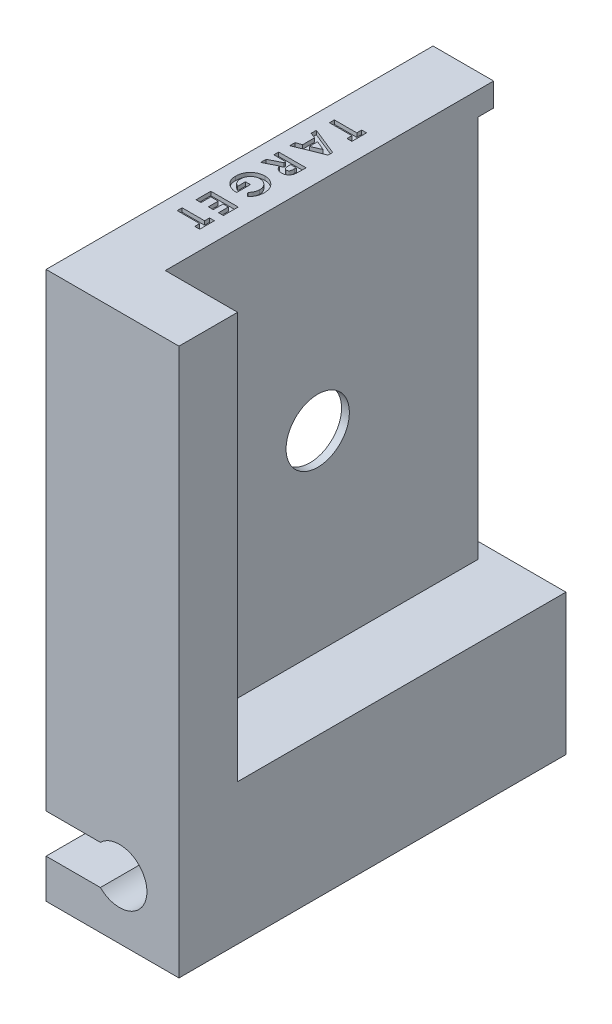
SolidWorks part; units mm, degrees
ref_plane "Plan de face" through (0, 0, 0) normal (0, 0, 1) x (1, 0, 0)
ref_plane "Plan de dessus" through (0, 0, 0) normal (0, 1, 0) x (1, 0, 0)
ref_plane "Plan de droite" through (0, 0, 0) normal (1, 0, 0) x (0, 0, -1)
sketch "Esquisse1" plane through (0, 0, 0) normal (0, 0, 1) x (1, 0, 0)
  line L1 (-8.5, -42.5) -> (8.5, -42.5)
  line L2 (-8.5, -42.5) -> (-8.5, 42.5)
  line L3 (-8.5, 42.5) -> (8.5, 42.5)
  line L4 (8.5, -42.5) -> (8.5, 42.5)
  line L5 (-8.5, -42.5) -> (8.5, 42.5) construction
  line L6 (-8.5, 42.5) -> (8.5, -42.5) construction
  point P0 (0, 0)
  dimension "D1" = 17
  dimension "D2" = 85
extrude "Boss.-Extru.1" add sketch "Esquisse1" along normal blind 49.5
sketch "Esquisse2" plane through (0, 0, 0) normal (0, 0, -1) x (-1, 0, 0)
  line L0 (8.5, 42.5) -> (8.5, -42.5) construction
  line L5 (7.55, 16.25) -> (5.75, 16.25)
  line L6 (7.55, 16.25) -> (7.55, -16.25)
  line L7 (7.55, -16.25) -> (5.75, -16.25)
  line L8 (5.75, 16.25) -> (5.75, -16.25)
  line L9 (7.55, 16.25) -> (5.75, -16.25) construction
  line L10 (7.55, -16.25) -> (5.75, 16.25) construction
  point P0 (6.65, 0)
  dimension "D1" = 1.8
  dimension "D2" = 32.5
  dimension "D3" = 0.95
extrude "Enlèv. mat.-Extru.1" cut sketch "Esquisse2" against normal blind 38.5
sketch "Esquisse3" plane through (0, 0, 0) normal (0, 0, -1) x (-1, 0, 0)
  line L0 (-8.5, -42.5) -> (-8.5, 42.5) construction
  line L1 (8.5, 24.5) -> (-8.5, 24.5)
  line L2 (8.5, 24.5) -> (8.5, -24.5)
  line L3 (8.5, -24.5) -> (-8.5, -24.5)
  line L4 (-8.5, 24.5) -> (-8.5, -24.5)
  line L5 (8.5, 24.5) -> (-8.5, -24.5) construction
  line L6 (8.5, -24.5) -> (-8.5, 24.5) construction
  point P0 (0, 0)
  dimension "D1" = 49
extrude "Enlèv. mat.-Extru.2" cut sketch "Esquisse3" against normal blind 2
sketch "Esquisse4" plane through (-8.5, 0, 0) normal (-1, 0, 0) x (0, 0, 1)
  line L0 (2, -24.5) -> (2, 24.5) construction
  circle A0 centre (22.5, 0) radius 16.25
  dimension "D1" = 32.5
  dimension "D2" = 20.5
extrude "Enlèv. mat.-Extru.3" cut sketch "Esquisse4" against normal through all
sketch "Esquisse5" plane through (-8.5, 0, 0) normal (-1, 0, 0) x (0, 0, 1)
  line L0 (7.0384, -5) -> (2, -5)
  line L1 (2, -24.5) -> (2, 24.5) construction
  line L2 (2, -5) -> (2, 5)
  line L3 (2, 5) -> (7.0384, 5)
  line L4 (7.0384, 5) -> (7.0384, -5)
  line L5 (49.5, -42.5) -> (0, -42.5) construction
  circle A0 centre (22.5, 0) radius 16.25 construction
  dimension "D1" = 10
  dimension "D2" = 37.5
extrude "Enlèv. mat.-Extru.4" cut sketch "Esquisse5" against normal through all
sketch "Esquisse6" plane through (0, 0, 0) normal (0, 0, -1) x (-1, 0, 0)
  line L0 (8.5, -32.5) -> (1.55, -32.5)
  line L1 (8.5, -24.5) -> (8.5, -42.5) construction
  line L2 (8.5, -32.5) -> (8.5, -37.5)
  line L3 (8.5, -37.5) -> (1.55, -37.5)
  line L4 (8.5, -42.5) -> (-8.5, -42.5) construction
  line L5 (-2.04, 0) -> (3.9749, 0) construction
  line L6 (8.5, 32.5) -> (8.5, 37.5)
  line L7 (8.5, 32.5) -> (1.55, 32.5)
  line L8 (8.5, 37.5) -> (1.55, 37.5)
  arc A0 (1.55, -37.5) -> (1.55, -32.5) centre (-0.8995, -35) cw
  arc A1 (1.55, 37.5) -> (1.55, 32.5) centre (-0.8995, 35) ccw
  dimension "D1" = 3.5
  dimension "D2" = 5
  dimension "D3" = 6.95
  dimension "D4" = 6.95
  dimension "D5" = 5
extrude "Enlèv. mat.-Extru.5" cut sketch "Esquisse6" against normal through all
sketch "Esquisse7" plane through (8.5, 0, 0) normal (1, 0, 0) x (0, 0, -1)
  line L5 (-2, 24.5) -> (-42, 24.5)
  line L6 (-2, 24.5) -> (-2, -24.5)
  line L7 (-2, -24.5) -> (-42, -24.5)
  line L8 (-42, 24.5) -> (-42, -24.5)
  dimension "D1" = 49
  dimension "D2" = 40
extrude "Enlèv. mat.-Extru.7" cut sketch "Esquisse7" against normal blind 13.25
sketch "Esquisse9" plane through (-4.75, 0, 0) normal (1, 0, 0) x (0, 0, -1)
  line L7 (-2, 5) -> (-2, 24.5)
  line L8 (-2, 24.5) -> (-42, 24.5)
  line L9 (-42, 24.5) -> (-42, -24.5)
  line L10 (-42, -24.5) -> (-2, -24.5)
  line L11 (-2, -24.5) -> (-2, -5)
  line L12 (-2, -5) -> (-7.0384, -5)
  line L13 (-7.0384, 5) -> (-2, 5)
  line L14 (-2, 5) -> (-2, 24.5)
  line L15 (-2, 24.5) -> (-42, 24.5)
  line L16 (-42, 24.5) -> (-42, -24.5)
  line L17 (-42, -24.5) -> (-2, -24.5)
  line L18 (-2, -24.5) -> (-2, -5)
  line L19 (-2, -5) -> (-7.0384, -5)
  line L20 (-7.0384, 5) -> (-2, 5)
  arc A1 (-7.0384, 5) -> (-7.0384, -5) centre (-22.5, 0) ccw
  arc A2 (-7.0384, 5) -> (-7.0384, -5) centre (-22.5, 0) ccw
  dimension "D1" = 0
extrude "Boss.-Extru.2" add sketch "Esquisse9" along normal blind 3
sketch "Esquisse10" plane through (-1.75, 0, 0) normal (1, 0, 0) x (0, 0, -1)
  line L1 (-2, -24.5) -> (-42, -24.5)
  line L2 (-2, -24.5) -> (-2, 24.5)
  line L3 (-2, 24.5) -> (-42, 24.5)
  line L4 (-42, -24.5) -> (-42, 24.5)
extrude "Boss.-Extru.3" add sketch "Esquisse10" along normal blind 1
sketch "Esquisse11" plane through (-1.75, 0, 0) normal (-1, 0, 0) x (0, 0, 1)
  circle A0 centre (22.5, 0) radius 4.05
  arc A1 (7.0384, -5) -> (7.0384, 5) centre (22.5, 0) ccw construction
  dimension "D1" = 8.1
extrude "Enlèv. mat.-Extru.9" cut sketch "Esquisse11" against normal through all
sketch "Esquisse12" plane through (0, 42.5, 0) normal (0, 1, 0) x (1, 0, 0)
  line L4 (8.5, 0) -> (-8.5, 0)
  line L5 (-8.5, 0) -> (-8.5, -49.5)
  line L6 (-8.5, -49.5) -> (8.5, -49.5)
  line L7 (8.5, -49.5) -> (8.5, 0)
  line L8 (8.5, 0) -> (-8.5, 0)
  line L9 (-8.5, 0) -> (-8.5, -49.5)
  line L10 (-8.5, -49.5) -> (8.5, -49.5)
  line L11 (8.5, -49.5) -> (8.5, 0)
  dimension "D1" = 0
extrude "Enlèv. mat.-Extru.10" cut sketch "Esquisse12" against normal blind 15
sketch "Esquisse13" plane through (8.5, 0, 0) normal (1, 0, 0) x (0, 0, -1)
  line L1 (-42, 24.5) -> (0, 24.5)
  line L2 (-42, 24.5) -> (-42, 27.5)
  line L3 (-42, 27.5) -> (0, 27.5)
  line L4 (0, 24.5) -> (0, 27.5)
extrude "Enlèv. mat.-Extru.11" cut sketch "Esquisse13" against normal up to surface (9.25 mm away) up to face at (-0.75, 0, 18.45)
sketch "Esquisse14" plane through (0, 27.5, 0) normal (0, 1, 0) x (1, 0, 0)
  line L0 (-6.625, 0) -> (-6.625, -49.5) construction
  line L1 (-0.75, 0) -> (-8.5, 0) construction
  line L2 (-8.5, -49.5) -> (8.5, -49.5) construction
  line L3 (-0.75, -42) -> (-0.75, 0) construction
  text T0 "<b>TARGET</b>" font "Century Gothic" height 3.5
  dimension "D1" = 5.875
extrude "Enlèv. mat.-Extru.12" cut sketch "Esquisse14" against normal blind 0.5
